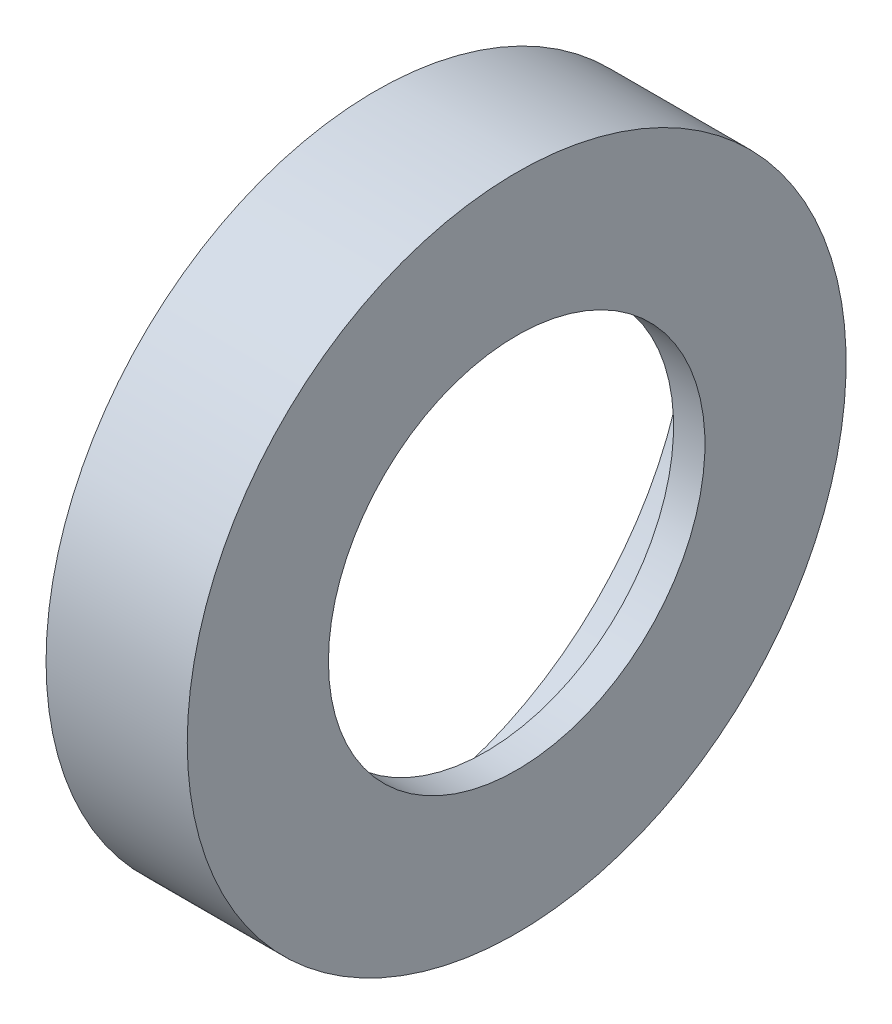
SolidWorks part; units mm, degrees
ref_plane "Plan de face" through (0, 0, 0) normal (0, 0, 1) x (1, 0, 0)
ref_plane "Plan de dessus" through (0, 0, 0) normal (0, 1, 0) x (1, 0, 0)
ref_plane "Plan de droite" through (0, 0, 0) normal (1, 0, 0) x (0, 0, -1)
sketch "Esquisse1" plane through (0, 0, 0) normal (0, 0, 1) x (1, 0, 0)
  line L0 (-32.8528, 0) -> (62.2997, 0) construction
  line L1 (0, 24) -> (0, 42)
  line L2 (0, 42) -> (-18, 42)
  line L3 (-18, 42) -> (-18, 40)
  line L4 (-18, 40) -> (-8, 40)
  line L5 (-8, 40) -> (-8, 37.65)
  line L6 (-8, 37.65) -> (-4, 37.65)
  line L7 (-4, 37.65) -> (-4, 24)
  line L8 (-4, 24) -> (0, 24)
  dimension "D1" = 4
  dimension "D2" = 4
  dimension "D3" = 10
  dimension "D4" = 42
  dimension "D5" = 24
  dimension "D6" = 37.65
  dimension "D7" = 40
revolve "Révolution1" add sketch "Esquisse1" angle 360 about L0
